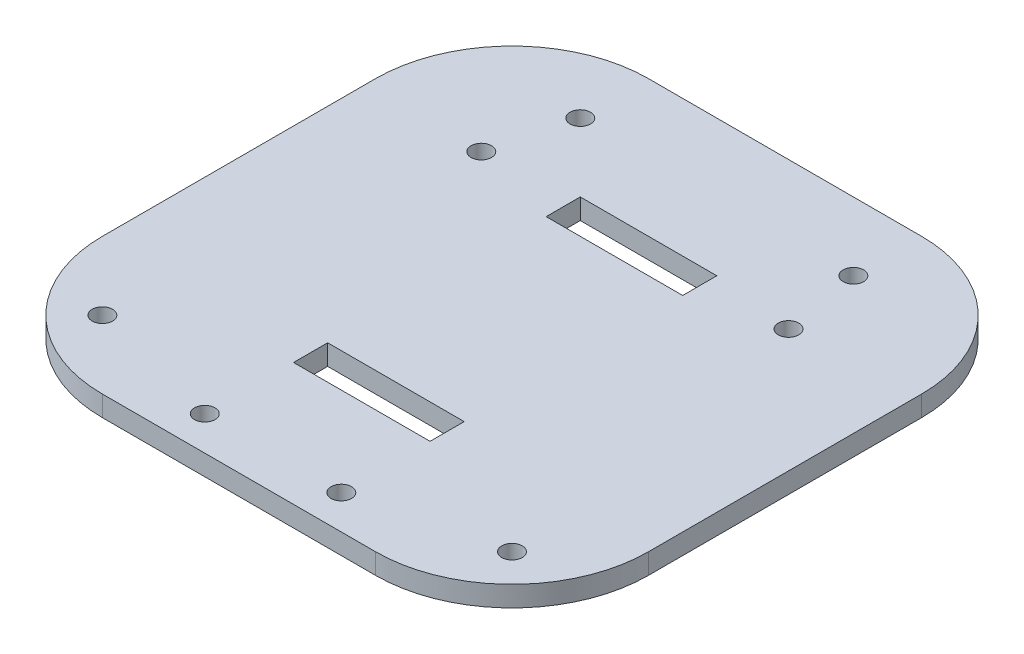
SolidWorks part; units mm, degrees
material "Pine"
ref_plane "Front Plane" through (0, 0, 0) normal (0, 0, 1) x (1, 0, 0)
ref_plane "Top Plane" through (0, 0, 0) normal (0, 1, 0) x (1, 0, 0)
ref_plane "Right Plane" through (0, 0, 0) normal (1, 0, 0) x (0, 0, -1)
sketch "Sketch3" plane through (0, 0, 0) normal (0, 1, 0) x (1, 0, 0)
  line L1 (0, 0) -> (80, 0)
  line L2 (0, 0) -> (0, 80)
  line L3 (0, 80) -> (80, 80)
  line L4 (80, 0) -> (80, 80)
  dimension "D1" = 80
  dimension "D2" = 80
extrude "Boss-Extrude1" add sketch "Sketch3" along normal blind 3
fillet "Fillet3" radius 20 1 edges at (0, 1.5, -80)
fillet "Fillet4" radius 20 1 edges at (80, 1.5, -80)
fillet "Fillet5" radius 20 1 edges at (80, 1.5, 0)
fillet "Fillet6" radius 20 1 edges at (0, 1.5, 0)
sketch "Sketch6" plane through (0, 3, 0) normal (0, 1, 0) x (1, 0, 0)
  line L4 (60, 80) -> (20, 80) construction
  line L5 (0, 60) -> (0, 20) construction
  line L6 (80, 20) -> (80, 60) construction
  circle A0 centre (17, 58.5) radius 1.5
  circle A1 centre (62, 58.5) radius 1.5
  dimension "D1" = 17
  dimension "D3" = 21.5
  dimension "D2" = 21.5
  dimension "D4" = 18
extrude "Cut-Extrude2" cut sketch "Sketch6" against normal blind 3
sketch "Sketch9" plane through (0, 3, 0) normal (0, 1, 0) x (1, 0, 0)
  line L4 (20, 0) -> (60, 0) construction
  line L5 (0, 60) -> (0, 20) construction
  line L6 (80, 20) -> (80, 60) construction
  circle A0 centre (70, 10) radius 1.5
  circle A1 centre (10, 10) radius 1.5
  dimension "D1" = 10
  dimension "D3" = 10
  dimension "D2" = 10
  dimension "D4" = 10
extrude "Cut-Extrude3" cut sketch "Sketch9" against normal blind 3
sketch "Sketch12" plane through (0, 3, 0) normal (0, 1, 0) x (1, 0, 0)
  line L0 (20, 0) -> (60, 0) construction
  line L1 (0, 60) -> (0, 20) construction
  line L2 (80, 20) -> (80, 60) construction
  circle A0 centre (30, 5) radius 1.5
  circle A1 centre (50, 5) radius 1.5
  dimension "D1" = 5
  dimension "D3" = 5
  dimension "D2" = 30
  dimension "D4" = 30
extrude "Cut-Extrude6" cut sketch "Sketch12" against normal blind 3
sketch "Sketch13" plane through (0, 3, 0) normal (0, 1, 0) x (1, 0, 0)
  line L0 (0, 60) -> (0, 20) construction
  line L1 (60, 80) -> (20, 80) construction
  line L2 (80, 20) -> (80, 60) construction
  circle A0 centre (20, 70) radius 1.5
  circle A1 centre (60, 70) radius 1.5
  dimension "D1" = 20
  dimension "D3" = 20
  dimension "D2" = 10
  dimension "D4" = 10
extrude "Cut-Extrude7" cut sketch "Sketch13" against normal blind 3
sketch "Sketch14" plane through (0, 3, 0) normal (0, 1, 0) x (1, 0, 0)
  line L0 (60, 80) -> (20, 80) construction
  line L1 (30, 60) -> (50, 60)
  line L2 (30, 60) -> (30, 55)
  line L3 (30, 55) -> (50, 55)
  line L4 (50, 60) -> (50, 55)
  line L5 (80, 20) -> (80, 60) construction
  line L6 (20, 0) -> (60, 0) construction
  line L7 (30, 23) -> (50, 23)
  line L8 (30, 23) -> (30, 18)
  line L9 (30, 18) -> (50, 18)
  line L10 (50, 23) -> (50, 18)
  line L11 (0, 60) -> (0, 20) construction
  dimension "D1" = 5
  dimension "D2" = 20
  dimension "20" = 20
  dimension "D3" = 5
  dimension "D4" = 30
  dimension "D5" = 20
  dimension "D6" = 18
  dimension "D7" = 30
extrude "Cut-Extrude8" cut sketch "Sketch14" against normal blind 10
